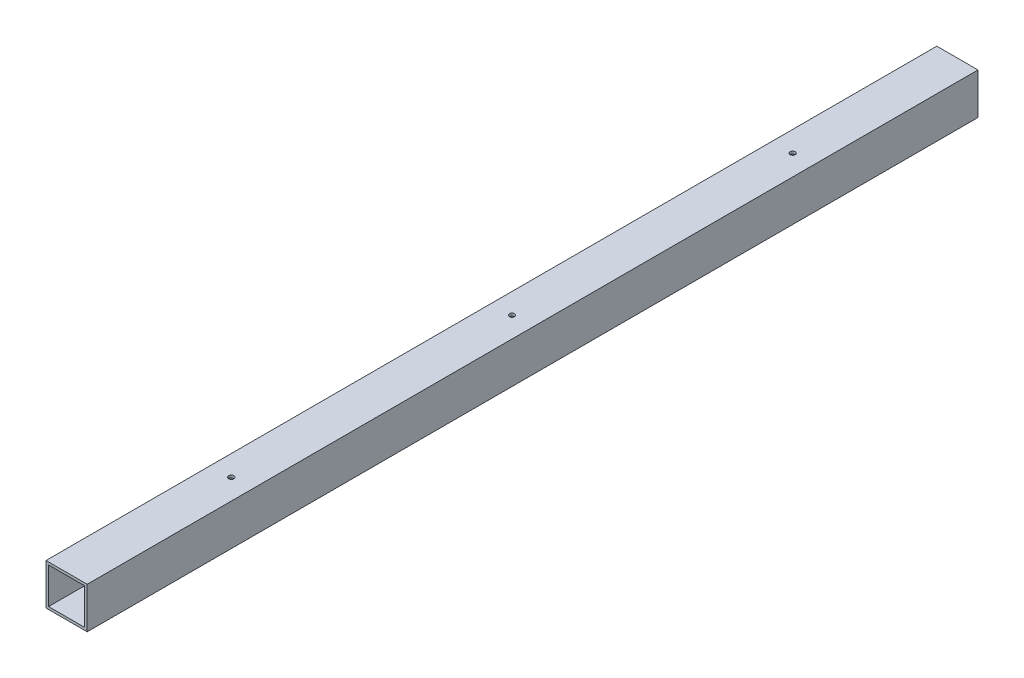
SolidWorks part; units mm, degrees
material "6061 Alloy"
ref_plane "Front Plane" through (0, 0, 0) normal (0, 0, 1) x (1, 0, 0)
ref_plane "Top Plane" through (0, 0, 0) normal (0, 1, 0) x (1, 0, 0)
ref_plane "Right Plane" through (0, 0, 0) normal (1, 0, 0) x (0, 0, -1)
sketch "Sketch1" plane through (0, 0, 0) normal (1, 0, 0) x (0, 0, -1)
  line L1 (-549.275, 25.4) -> (549.275, 25.4)
  line L2 (-549.275, 25.4) -> (-549.275, -25.4)
  line L3 (-549.275, -25.4) -> (549.275, -25.4)
  line L4 (549.275, 25.4) -> (549.275, -25.4)
  line L5 (-549.275, 25.4) -> (549.275, -25.4) construction
  line L6 (-549.275, -25.4) -> (549.275, 25.4) construction
  point P0 (0, 0)
  dimension "D1" = 1098.55
  dimension "D2" = 50.8
extrude "Boss-Extrude1" add sketch "Sketch1" along normal blind 50.8
sketch "Sketch2" plane through (0, 0, 549.275) normal (0, 0, 1) x (1, 0, 0)
  line L8 (3.175, 22.225) -> (3.175, -22.225)
  line L9 (3.175, -22.225) -> (47.625, -22.225)
  line L10 (47.625, -22.225) -> (47.625, 22.225)
  line L11 (47.625, 22.225) -> (3.175, 22.225)
  line L12 (3.175, 22.225) -> (3.175, -22.225)
  line L13 (3.175, -22.225) -> (47.625, -22.225)
  line L14 (47.625, -22.225) -> (47.625, 22.225)
  line L15 (47.625, 22.225) -> (3.175, 22.225)
  dimension "D1" = 3.175
extrude "Cut-Extrude1" cut sketch "Sketch2" against normal through all
sketch "Sketch5" plane through (0, 25.4, 0) normal (0, 1, 0) x (1, 0, 0)
  line L0 (0, 549.275) -> (0, -549.275) construction
  line L1 (50.8, -549.275) -> (0, -549.275) construction
  line L2 (50.8, 549.275) -> (0, 549.275) construction
  line L3 (50.8, 549.275) -> (50.8, -549.275) construction
  circle A3 centre (25.4, -346.075) radius 3.302
  circle A4 centre (25.4, 0) radius 3.175
  circle A5 centre (25.4, 346.075) radius 3.175
  dimension "D1" = 6.604
  dimension "D4" = 6.35
  dimension "D5" = 6.35
  dimension "D2" = 25.4
  dimension "D3" = 203.2
  dimension "D6" = 203.2
  dimension "D7" = 346.075
  dimension "D8" = 25.4
extrude "Cut-Extrude2" cut sketch "Sketch5" against normal blind 50.8
